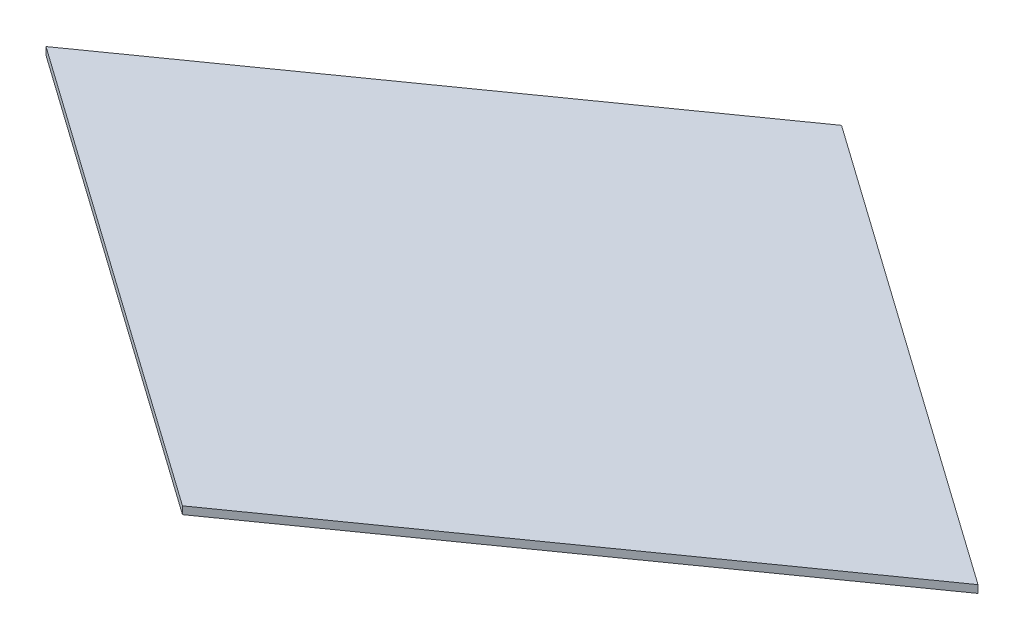
SolidWorks part; units mm, degrees
ref_plane "Front Plane" through (0, 0, 0) normal (0, 0, 1) x (1, 0, 0)
ref_plane "Top Plane" through (0, 0, 0) normal (0, 1, 0) x (1, 0, 0)
ref_plane "Right Plane" through (0, 0, 0) normal (1, 0, 0) x (0, 0, -1)
sketch "Sketch1" plane through (0, 0, 0) normal (0, 1, 0) x (1, 0, 0)
  line L0 (-152.4, 0) -> (0, 107.7631)
  line L1 (0, 107.7631) -> (152.4, 0)
  line L2 (152.4, 0) -> (0, -107.7631)
  line L3 (0, -107.7631) -> (-152.4, 0)
  line L4 (-152.4, 0) -> (152.4, 0) construction
  line L5 (0, 107.7631) -> (0, -107.7631) construction
  point P2 (0, 0)
  dimension "D1" = 70.529
  dimension "D2" = 304.8
extrude "Boss-Extrude1" add sketch "Sketch1" along normal mid plane 2.5
equation "\"D1@Sketch1\"=arccos( 1/3)"
